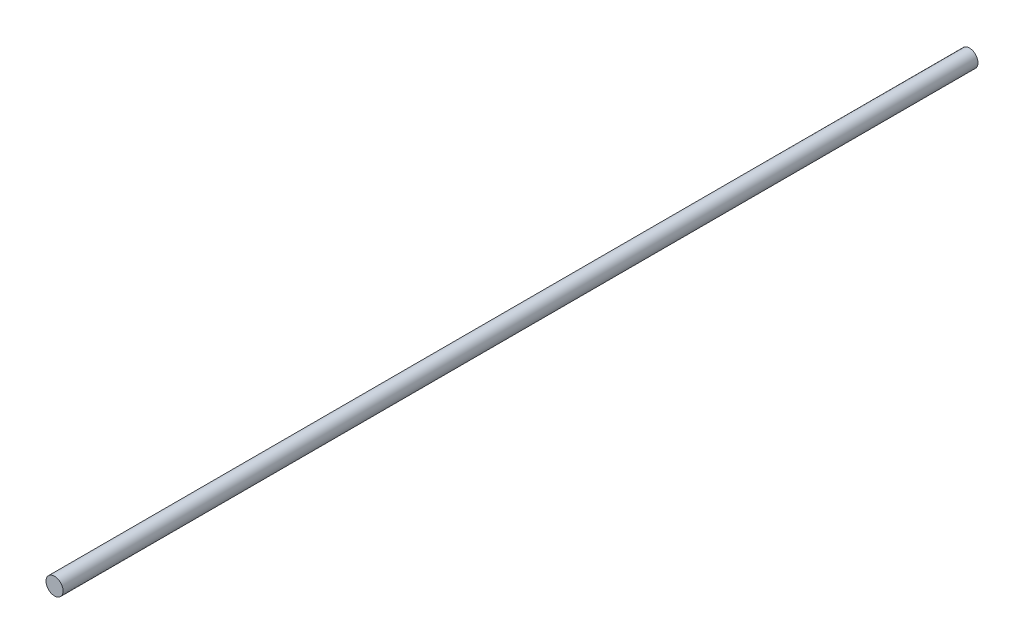
SolidWorks part; units mm, degrees
ref_plane "前视基准面" through (0, 0, 0) normal (0, 0, 1) x (1, 0, 0)
ref_plane "上视基准面" through (0, 0, 0) normal (0, 1, 0) x (1, 0, 0)
ref_plane "右视基准面" through (0, 0, 0) normal (1, 0, 0) x (0, 0, -1)
sketch "草图1" plane through (0, 0, 0) normal (0, 0, 1) x (1, 0, 0)
  circle A0 centre (0, 0) radius 4
  dimension "D1" = 8
extrude "凸台-拉伸1" add sketch "草图1" along normal blind 428
